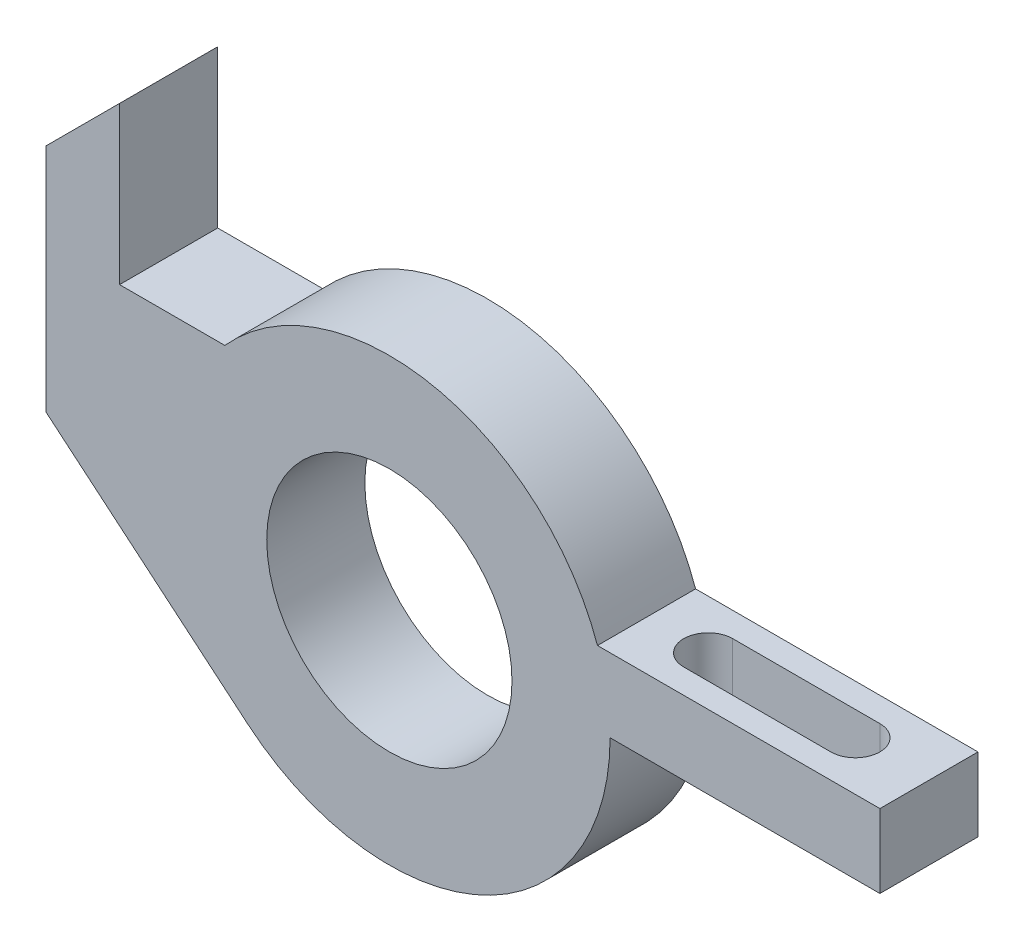
SolidWorks part; units mm, degrees
ref_plane "Front Plane" through (0, 0, 0) normal (0, 0, 1) x (1, 0, 0)
ref_plane "Top Plane" through (0, 0, 0) normal (0, 1, 0) x (1, 0, 0)
ref_plane "Right Plane" through (0, 0, 0) normal (1, 0, 0) x (0, 0, -1)
sketch "Sketch1" plane through (0, 0, 0) normal (0, 0, 1) x (1, 0, 0)
  line L0 (-70, 0) -> (-28.9286, -34.4694)
  line L1 (42.4264, 15) -> (100, 15)
  line L4 (100, 15) -> (100, 0)
  line L5 (-70, 0) -> (-70, 47)
  line L6 (-70, 47) -> (-55, 62)
  line L7 (-55, 62) -> (-55, 30)
  line L8 (-55, 30) -> (-33.541, 30)
  line L9 (45, 0) -> (100, 0)
  arc A0 (42.4264, 15) -> (-33.541, 30) centre (0, 0) ccw
  circle A1 centre (0, 0) radius 25
  arc A2 (-28.9286, -34.4694) -> (45, 0) centre (0, 0) ccw
  point P4 (0, 0)
  point P6 (0, 0)
  point P8 (0, 0)
  point P15 (0, 0)
  point P16 (0, 0)
  point P18 (44.9304, 0)
  point P19 (45, -11.1113)
  point P20 (45, -13.9643)
  dimension "D1" = 90
  dimension "D2" = 50
  dimension "D3" = 15
  dimension "D4" = 100
  dimension "D5" = 70
  dimension "D6" = 30
  dimension "D7" = 17
  dimension "D8" = 32
  dimension "D9" = 15
extrude "Boss-Extrude1" add sketch "Sketch1" along normal blind 20
sketch "Sketch2" plane through (0, 15, 0) normal (0, 1, 0) x (1, 0, 0)
  line L0 (100, -20) -> (100, 0) construction
  line L1 (55, -15) -> (85, -15)
  line L3 (55, -5) -> (85, -5)
  arc A0 (55, -5) -> (55, -15) centre (55, -10) ccw
  arc A1 (85, -15) -> (85, -5) centre (85, -10) ccw
  point P5 (0, 0)
  point P10 (850, -106.1058)
  point P11 (100, -10)
  dimension "D1" = 10
  dimension "D2" = 15
  dimension "D3" = 30
extrude "Cut-Extrude1" cut sketch "Sketch2" against normal through all
